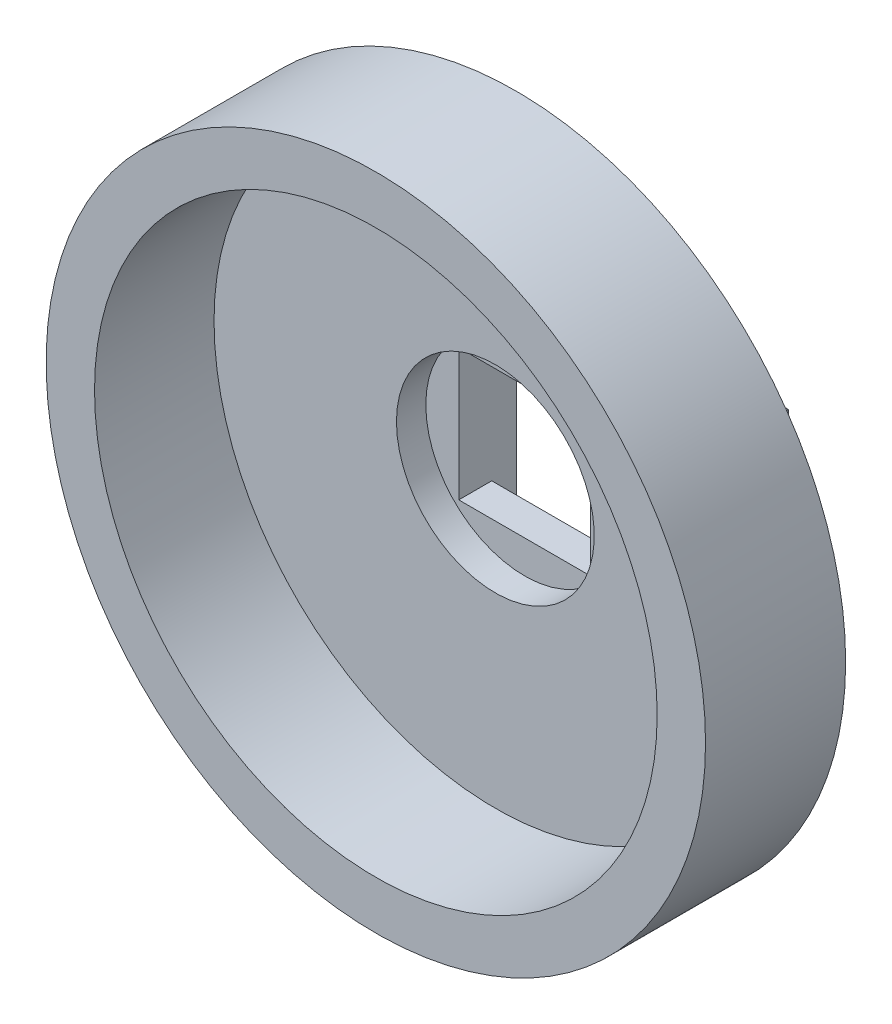
SolidWorks part; units mm, degrees
material "1060 Alloy"
ref_plane "Front Plane" through (0, 0, 0) normal (0, 0, 1) x (1, 0, 0)
ref_plane "Top Plane" through (0, 0, 0) normal (0, 1, 0) x (1, 0, 0)
ref_plane "Right Plane" through (0, 0, 0) normal (1, 0, 0) x (0, 0, -1)
sketch "Sketch1" plane through (0, 0, 0) normal (0, 0, 1) x (1, 0, 0)
  line L1 (0, 0) -> (25, 0)
  line L2 (0, 0) -> (0, 15)
  line L3 (0, 15) -> (25, 15)
  line L4 (25, 0) -> (25, 15)
  dimension "D1" = 25
  dimension "D2" = 15
extrude "Boss-Extrude1" add sketch "Sketch1" along normal blind 4.03
hole_wizard "M2 Tapped Hole1" positions "Sketch3" profile "Sketch4" tap size "M2" standard "ISO"
sketch "Sketch3" plane through (0, 0, 0) normal (0, 0, -1) x (-1, 0, 0)
  line L0 (-25, 0) -> (-25, 15) construction
  line L2 (-25, 15) -> (0, 15) construction
  line L3 (0, 15) -> (0, 0) construction
  point P0 (-23, 7.5)
  point P2 (-2, 7.5)
  dimension "D1" = 21
  dimension "D2" = 2
  dimension "D3" = 7.5
  dimension "D4" = 7.5
  dimension "D5" = 2
sketch "Sketch4" plane through (23, 7.5, 0) normal (1, 0, 0) x (0, 1, 0)
  line L0 (0, 0) -> (0, 3.4807)
  line L1 (0, 3.4807) -> (0.8, 3)
  line L2 (0.8, 3) -> (0.8, 0)
  line L5 (0.8, 0) -> (0, 0)
  line L10 (0, 3.4807) -> (-0.8, 3) construction
  line L11 (0, -6.35) -> (0, 107.95) construction
  dimension "Tap Drill Dia." = 1.6
  dimension "Tap Drill Depth" = 3
  dimension "Drill Angle" = 118
cosmetic thread "Hole Thread1" parameters "D1"=3, "D2"=2
cosmetic thread "Hole Thread2" parameters "D1"=3, "D2"=2
sketch "Sketch5" plane through (0, 0, 4.03) normal (0, 0, 1) x (1, 0, 0)
  circle A0 centre (12.5, 7.5) radius 20
  dimension "D1" = 40
extrude "Boss-Extrude2" add sketch "Sketch5" along normal blind 8.5
sketch "Sketch6" plane through (0, 0, 12.53) normal (0, 0, 1) x (1, 0, 0)
  circle A0 centre (12.5, 7.5) radius 12.25
  dimension "D1" = 24.5
extrude "Cut-Extrude1" cut sketch "Sketch6" against normal blind 5.25
hole_wizard "1-1/2-6 Tapped Hole1" positions "Sketch8" profile "Sketch7" tap size "1-1/2-6" standard "ANSI Inch"
sketch "Sketch8" plane through (0, 0, 12.53) normal (0, 0, 1) x (1, 0, 0)
  point P0 (12.5, 7.5)
sketch "Sketch7" plane through (12.5, 7.5, 12.53) normal (1, 0, 0) x (0, -1, 0)
  line L0 (0, 0) -> (0, 7.25)
  line L1 (0, 7.25) -> (17.0663, 7.25)
  line L2 (17.0663, 7.25) -> (17.0663, 0)
  line L5 (17.0663, 0) -> (0, 0)
  line L10 (0, 7.25) -> (-17.0663, 7.25) construction
  line L11 (0, -6.35) -> (0, 107.95) construction
  dimension "Tap Drill Dia." = 34.1325
  dimension "Tap Drill Depth" = 7.25
  dimension "Drill Angle" = 180
cosmetic thread "Hole Thread3" parameters "D1"=7.25, "D2"=38.1
sketch "Sketch13" plane through (0, 0, 0) normal (0, 0, -1) x (-1, 0, 0)
  line L0 (-12.5, 15) -> (-12.5, 0)
  line L1 (-25, 15) -> (0, 15) construction
  line L2 (0, 0) -> (-25, 0) construction
  line L3 (-12.5, 7.5) -> (-12.5, 7.75)
  line L5 (-8.5, 3.75) -> (-16.5, 3.75)
  line L6 (-8.5, 3.75) -> (-8.5, 11.75)
  line L7 (-8.5, 11.75) -> (-16.5, 11.75)
  line L8 (-16.5, 3.75) -> (-16.5, 11.75)
  dimension "D1" = 0.25
  dimension "D2" = 8
  dimension "D3" = 8
extrude "Cut-Extrude2" cut sketch "Sketch13" against normal blind 3.5 contours L8 L5 L0 L7 | L6 L7 L0 L5
sketch "Sketch14" plane through (0, 3.75, 0) normal (0, 1, 0) x (1, 0, 0)
  line L0 (8.5, -3.5) -> (8.5, 0) construction
  line L1 (16.5, 0) -> (8.5, 0)
  line L2 (16.5, 0) -> (16.5, -1.5)
  line L3 (16.5, -1.5) -> (8.5, -1.5)
  line L4 (8.5, 0) -> (8.5, -1.5)
  dimension "D1" = 1.5
extrude "Cut-Extrude3" cut sketch "Sketch14" against normal blind 13.5
sketch "Sketch15" plane through (0, 0, 3.5) normal (0, 0, -1) x (-1, 0, 0)
  circle A0 centre (-12.5, 7.75) radius 6
  dimension "D1" = 12
extrude "Cut-Extrude4" cut sketch "Sketch15" against normal blind 13.5
